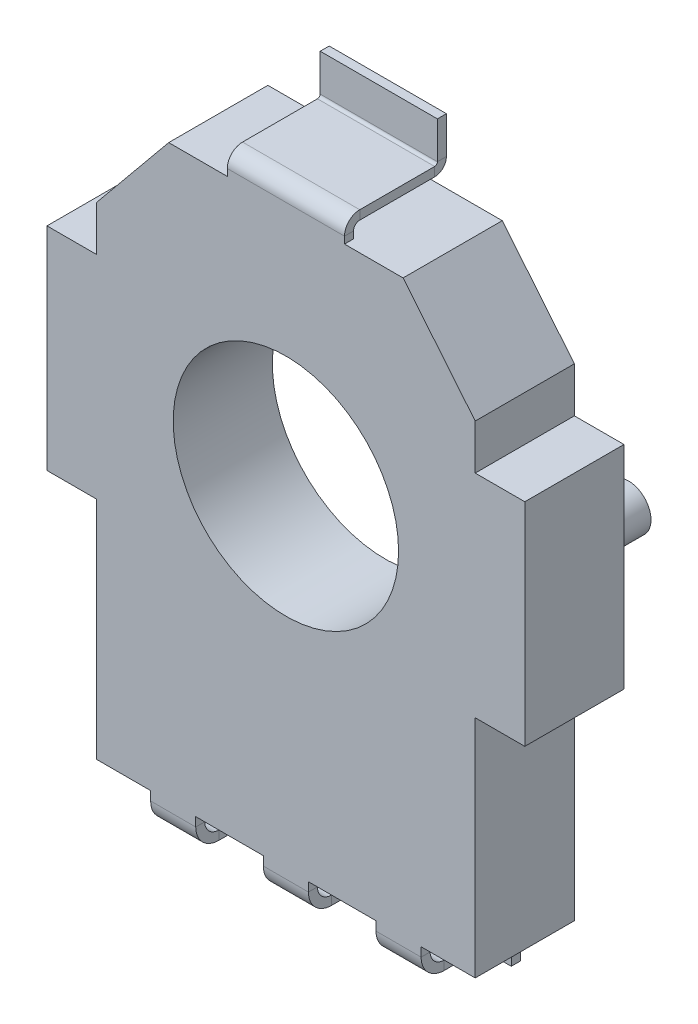
SolidWorks part; units mm, degrees
ref_plane "Front Plane" through (0, 0, 0) normal (0, 0, 1) x (1, 0, 0)
ref_plane "Top Plane" through (0, 0, 0) normal (0, 1, 0) x (1, 0, 0)
ref_plane "Right Plane" through (0, 0, 0) normal (1, 0, 0) x (0, 0, -1)
sketch "Sketch1" plane through (0, 0, 0) normal (0, 0, 1) x (1, 0, 0)
  line L0 (0, 5.3) -> (2.6, 5.3)
  line L1 (2.6, 5.3) -> (4.2, 3.35)
  line L2 (4.2, 3.35) -> (4.2, 2.35)
  line L3 (4.2, 2.35) -> (5.3, 2.35)
  line L4 (5.3, 2.35) -> (5.3, -2.35)
  line L5 (5.3, -2.35) -> (4.2, -2.35)
  line L6 (4.2, -2.35) -> (4.2, -7.35)
  line L7 (4.2, -7.35) -> (0, -7.35)
  line L8 (0, -7.35) -> (0, -2.5)
  line L9 (0, 5.3) -> (0, 2.5)
  arc A0 (0, -2.5) -> (0, 2.5) centre (0, 0) ccw
  point P19 (5.3, 0)
  dimension "D1" = 5
  dimension "D2" = 4.2
  dimension "D3" = 5.3
  dimension "D4" = 7.35
  dimension "D5" = 5.3
  dimension "D6" = 1
  dimension "D8" = 2.6
  dimension "D9" = 5
extrude "Boss-Extrude1" add sketch "Sketch1" along normal blind 2.2
mirror "Mirror1" about plane through (0, -7.35, 2.2) normal (1, 0, 0) of "Boss-Extrude1"
sketch "Sketch2" plane through (0, -7.35, 0) normal (0, -1, 0) x (1, 0, 0)
  line L0 (-4.2, 2.2) -> (4.2, 2.2) construction
  line L1 (-3, 2.2) -> (-2, 2.2)
  line L2 (-3, 2.2) -> (-3, 2)
  line L3 (-3, 2) -> (-2, 2)
  line L4 (-2, 2.2) -> (-2, 2)
  line L6 (-0.5, 2.2) -> (0.5, 2.2)
  line L7 (-0.5, 2.2) -> (-0.5, 2)
  line L8 (-0.5, 2) -> (0.5, 2)
  line L9 (0.5, 2.2) -> (0.5, 2)
  line L10 (2, 2.2) -> (3, 2.2)
  line L11 (2, 2.2) -> (2, 2)
  line L12 (2, 2) -> (3, 2)
  line L13 (3, 2.2) -> (3, 2)
  point P14 (-2.5, 2)
  point P15 (0, 2)
  point P16 (2.5, 2)
  dimension "D1" = 1
  dimension "D2" = 2.5
  dimension "D3" = 2.5
  dimension "D4" = 0.2
sketch "Sketch3" plane through (0, 0, 0) normal (1, 0, 0) x (0, 0, -1)
  line L0 (-2, -7.35) -> (-2, -7.5495)
  line L1 (-1.687, -7.8624) -> (-0.313, -7.8624)
  line L2 (0, -8.1754) -> (0, -8.725)
  line L3 (0, -7.35) -> (0, -2.35) construction
  line L4 (0, -8.725) -> (0, -7.35) construction
  line L5 (0, 5.3) -> (0, 6.675) construction
  arc A0 (-2, -7.5495) -> (-1.687, -7.8624) centre (-1.687, -7.5495) ccw
  arc A1 (-0.313, -7.8624) -> (0, -8.1754) centre (-0.313, -8.1754) cw
  dimension "D1" = 15.4
sweep "Sweep1" add profiles "Sketch2" path "Sketch3"
sketch "Sketch4" plane through (0, 5.3, 0) normal (0, 1, 0) x (1, 0, 0)
  line L1 (-1.3, -2.2) -> (1.3, -2.2)
  line L2 (-1.3, -2.2) -> (-1.3, -2)
  line L3 (-1.3, -2) -> (1.3, -2)
  line L4 (1.3, -2.2) -> (1.3, -2)
  point P6 (0, -2.2)
  dimension "D1" = 2.6
  dimension "D2" = 0.2
sketch "Sketch5" plane through (0, 0, 0) normal (1, 0, 0) x (0, 0, -1)
  line L0 (-2.061, 5.3) -> (-2.061, 5.452)
  line L1 (-2.2, 5.3) -> (-2, 5.3) construction
  line L2 (-2.2, 5.3) -> (-2, 5.3) construction
  line L3 (-1.8613, 5.6517) -> (-0.1997, 5.6517)
  line L4 (0, 5.3) -> (0, 6.675) construction
  line L5 (0, 5.8514) -> (0, 6.675)
  arc A0 (-2.061, 5.452) -> (-1.8613, 5.6517) centre (-1.8613, 5.452) cw
  arc A1 (-0.1997, 5.6517) -> (0, 5.8514) centre (-0.1997, 5.8514) ccw
sweep "Sweep2" add profiles "Sketch4" path "Sketch5"
sketch "Sketch6" plane through (0, 0, 0) normal (0, 0, -1) x (-1, 0, 0)
  circle A0 centre (-4.2, 0) radius 0.5
  circle A1 centre (4.2, 0) radius 0.5
  dimension "D1" = 1
extrude "Boss-Extrude2" add sketch "Sketch6" along normal blind 1.2
